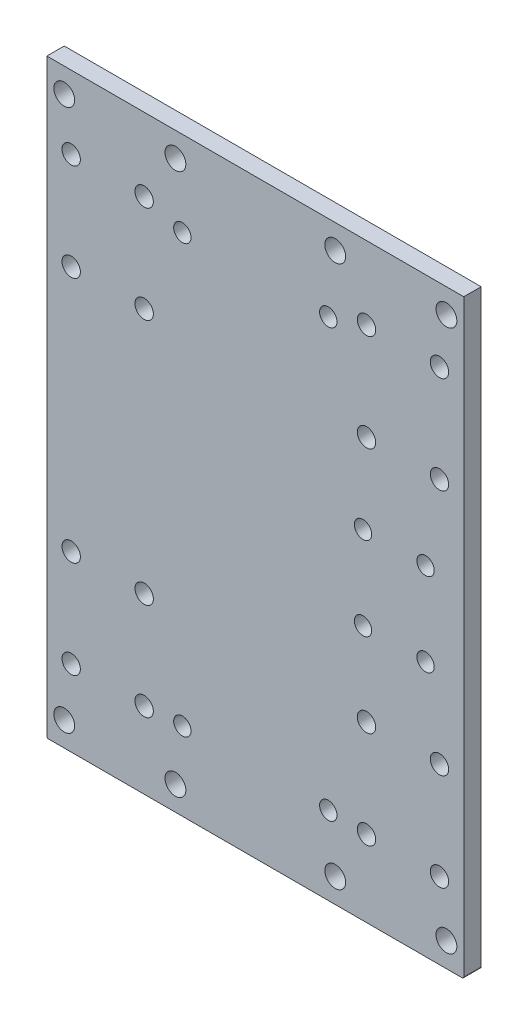
SolidWorks part; units mm, degrees
ref_plane "Front Plane" through (0, 0, 0) normal (0, 0, 1) x (1, 0, 0)
ref_plane "Top Plane" through (0, 0, 0) normal (0, 1, 0) x (1, 0, 0)
ref_plane "Right Plane" through (0, 0, 0) normal (1, 0, 0) x (0, 0, -1)
sketch "Sketch1" plane through (0, 0, 0) normal (0, 0, 1) x (1, 0, 0)
  line L1 (0, 0) -> (120, 0)
  line L2 (0, 0) -> (0, 170)
  line L3 (0, 170) -> (120, 170)
  line L4 (120, 0) -> (120, 170)
  circle A0 centre (28, 22) radius 2.65
  circle A1 centre (7, 22) radius 2.65
  circle A3 centre (7, 50) radius 2.65
  circle A4 centre (28, 50) radius 2.65
  circle A13 centre (28, 121) radius 2.65
  circle A14 centre (7, 121) radius 2.65
  circle A16 centre (28, 149) radius 2.65
  circle A17 centre (7, 149) radius 2.65
  circle A22 centre (39, 22.5) radius 2.5
  circle A23 centre (81, 22.5) radius 2.5
  circle A24 centre (5, 163) radius 3
  circle A25 centre (115, 163) radius 3
  circle A26 centre (37, 163) radius 3
  circle A27 centre (83, 163) radius 3
  circle A28 centre (115, 7) radius 3
  circle A29 centre (83, 7) radius 3
  circle A30 centre (37, 7) radius 3
  circle A31 centre (5, 7) radius 3
  circle A32 centre (39, 145.5) radius 2.5
  circle A33 centre (81, 145.5) radius 2.5
  circle A34 centre (113, 149) radius 2.65
  circle A35 centre (92, 149) radius 2.65
  circle A36 centre (92, 121) radius 2.65
  circle A37 centre (113, 121) radius 2.65
  circle A38 centre (92, 50) radius 2.65
  circle A39 centre (113, 50) radius 2.65
  circle A40 centre (113, 22) radius 2.65
  circle A41 centre (92, 22) radius 2.65
  circle A46 centre (109, 97.5) radius 2.5
  circle A47 centre (109, 73.5) radius 2.5
  circle A48 centre (91, 73.5) radius 2.5
  circle A49 centre (91, 97.5) radius 2.5
extrude "Boss-Extrude1" add sketch "Sketch1" along normal blind 5
fillet "Fillet1" radius 0.5 2 edges at (0, 0, 2.5) (120, 0, 2.5)
